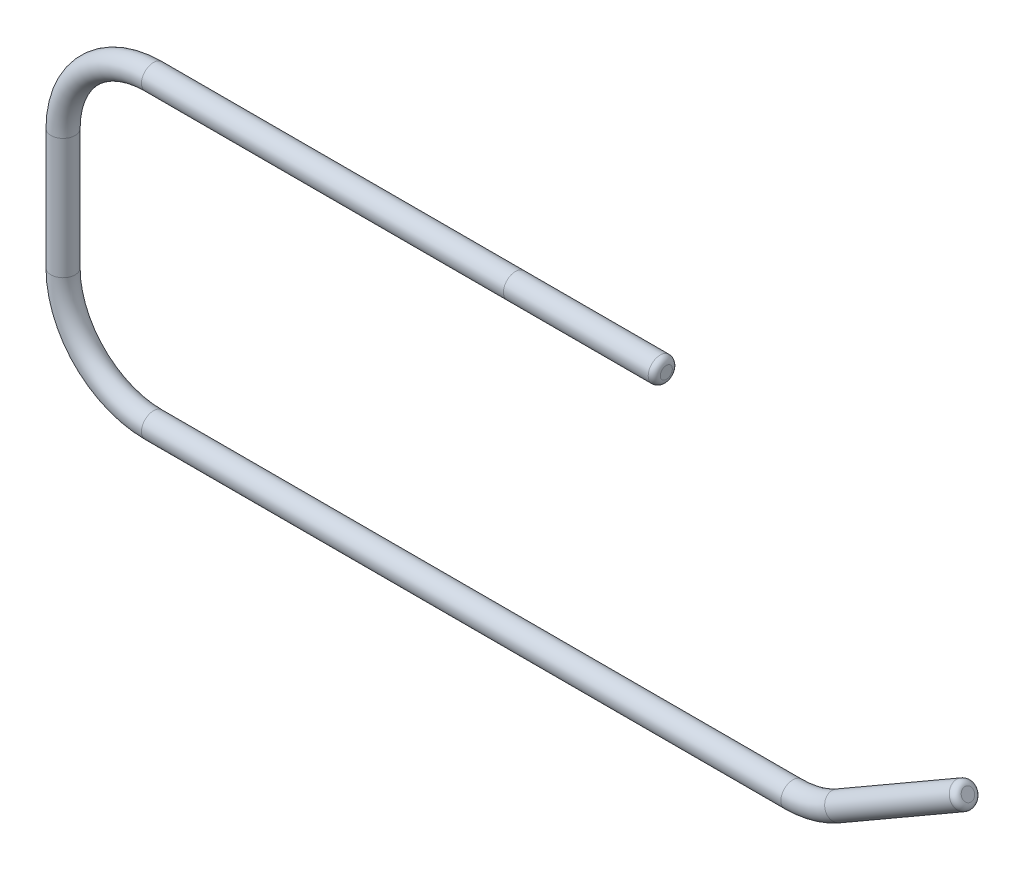
SolidWorks part; units mm, degrees
material "1.4301 (X5CrNi18-10)"
ref_plane "Front Plane" through (0, 0, 0) normal (0, 0, 1) x (1, 0, 0)
ref_plane "Top Plane" through (0, 0, 0) normal (0, 1, 0) x (1, 0, 0)
ref_plane "Right Plane" through (0, 0, 0) normal (1, 0, 0) x (0, 0, -1)
sketch "Sketch1" plane through (0, 0, 0) normal (0, 0, 1) x (1, 0, 0)
  line L0 (0, 0) -> (-120, 0)
  line L1 (55, 0) -> (-55, 0) construction
  line L2 (-150, -30) -> (-150, -70)
  line L3 (-120, -100) -> (91.9615, -100)
  line L4 (106.9615, -95.9808) -> (150, -71.1325)
  line L5 (0, 0) -> (50, 0)
  arc A0 (91.9615, -100) -> (106.9615, -95.9808) centre (91.9615, -70) ccw
  arc A1 (-150, -70) -> (-120, -100) centre (-120, -70) ccw
  arc A2 (-120, 0) -> (-150, -30) centre (-120, -30) ccw
  point P11 (100, -100)
  point P14 (-150, -100)
  point P17 (-150, 0)
  dimension "D7" = 30
  dimension "D1" = 100
  dimension "D2" = 150
  dimension "D3" = 300
  dimension "D4" = 250
  dimension "D5" = 150
  dimension "D6" = 50
ref_plane "Plane1" through (50, 0, 0) normal (1, 0, 0) x (0, 0, -1)
sweep "Sweep1" add path "Sketch1" circular profile diameter 8 parameters "D3"=8
fillet "Fillet1" radius 2 2 edges at (50, 4, 0) (152, -74.5966, 0)
